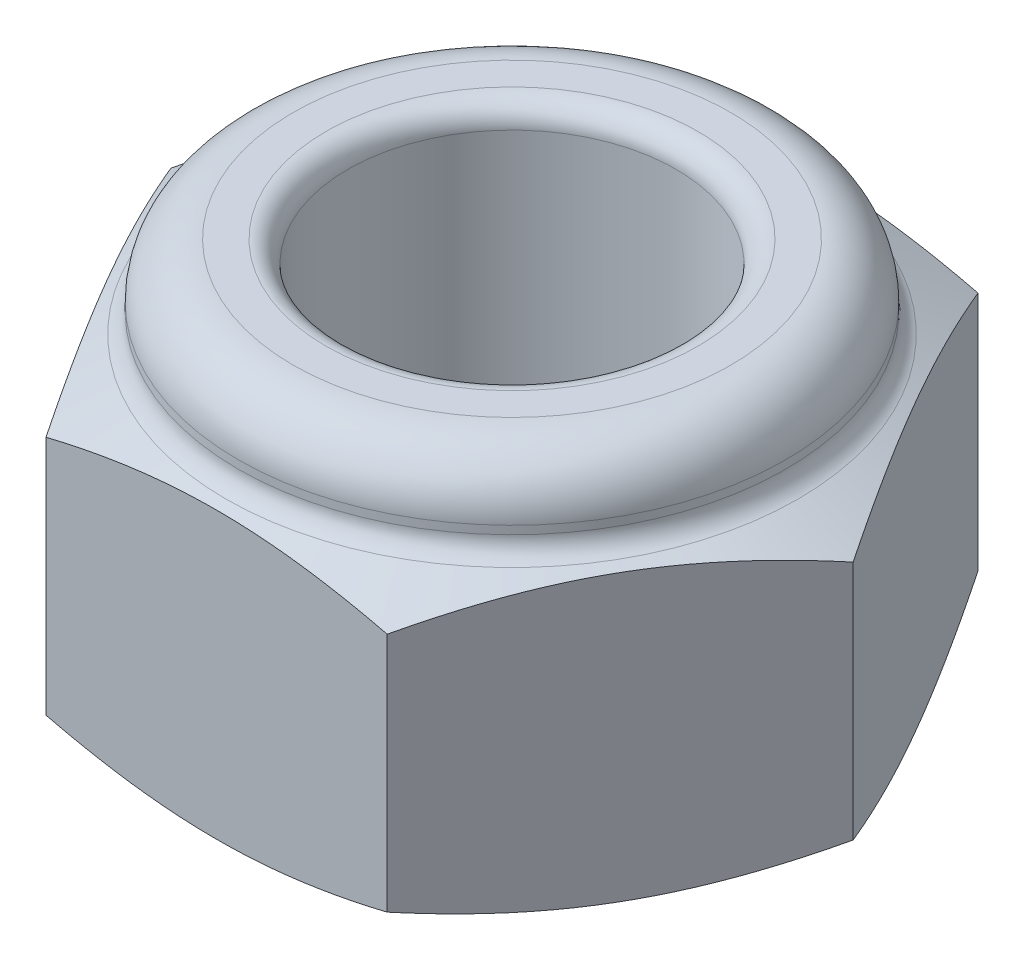
SolidWorks part; units mm, degrees
ref_plane "前视基准面" through (0, 0, 0) normal (0, 0, 1) x (1, 0, 0)
ref_plane "上视基准面" through (0, 0, 0) normal (0, 1, 0) x (1, 0, 0)
ref_plane "右视基准面" through (0, 0, 0) normal (1, 0, 0) x (0, 0, -1)
sketch "草图1" plane through (0, 0, 0) normal (0, 1, 0) x (1, 0, 0)
  line L1 (3.1177, 0) -> (1.5588, 2.7)
  line L2 (1.5588, 2.7) -> (-1.5588, 2.7)
  line L3 (-1.5588, 2.7) -> (-3.1177, 0)
  line L4 (-3.1177, 0) -> (-1.5588, -2.7)
  line L5 (-1.5588, -2.7) -> (1.5588, -2.7)
  line L6 (1.5588, -2.7) -> (3.1177, 0)
  circle A0 centre (0, 0) radius 2.7 construction
  dimension "D1" = 5.4
extrude "凸台-拉伸1" add sketch "草图1" along normal mid plane 2.8
sketch "草图2" plane through (0, 0, 0) normal (0, 0, 1) x (1, 0, 0)
  line L0 (-3.1177, 1.1) -> (-2.5, 1.4)
  line L1 (-3.1177, 1.4) -> (-3.1177, -1.4) construction
  line L2 (-3.1177, 1.4) -> (-1.5588, 1.4) construction
  line L3 (-2.5, 1.4) -> (-3.1177, 1.4)
  line L4 (-3.1177, 1.4) -> (-3.1177, 1.1)
  line L5 (0, 0) -> (0, 1.4) construction
  line L6 (-1.5588, 1.4) -> (1.5588, 1.4) construction
  dimension "D1" = 5
  dimension "D2" = 0.3
revolve "切除-旋转1" cut sketch "草图2" angle 360 about L5
mirror "镜向3" about plane through (0, 0, 0) normal (0, 1, 0) of "切除-旋转1"
sketch "草图3" plane through (0, 1.4, 0) normal (0, 1, 0) x (1, 0, 0)
  circle A0 centre (0, 0) radius 1.5
  dimension "D1" = 3
extrude "切除-拉伸1" cut sketch "草图3" against normal through all
sketch "草图4" plane through (0, 0, 0) normal (1, 0, 0) x (0, 0, -1)
  line L0 (-2.5, 1.4) -> (-2.5, 1.6)
  line L1 (-2, 2.1) -> (-1.5, 2.1)
  line L2 (-1.5, 2.1) -> (-1.5, 1.4)
  line L3 (2.5, 1.4) -> (-2.5, 1.4) construction
  line L4 (-1.5, 1.4) -> (-2.5, 1.4)
  line L5 (0, 1.4) -> (0, -1.4) construction
  line L6 (1.5, 1.4) -> (-1.5, 1.4) construction
  line L7 (-2.5, -1.4) -> (2.5, -1.4) construction
  arc A0 (-2.5, 1.6) -> (-2, 2.1) centre (-2, 1.6) cw
  point P15 (-1.772, 2)
  dimension "D1" = 3
  dimension "D2" = 3.5
  dimension "D3" = 0.2
  dimension "D4" = 0.5
revolve "旋转1" add sketch "草图4" angle 360 about L5
fillet "圆角1" radius 0.2 2 edges at (0, 1.4, 2.5) (0, 2.1, 1.5)
